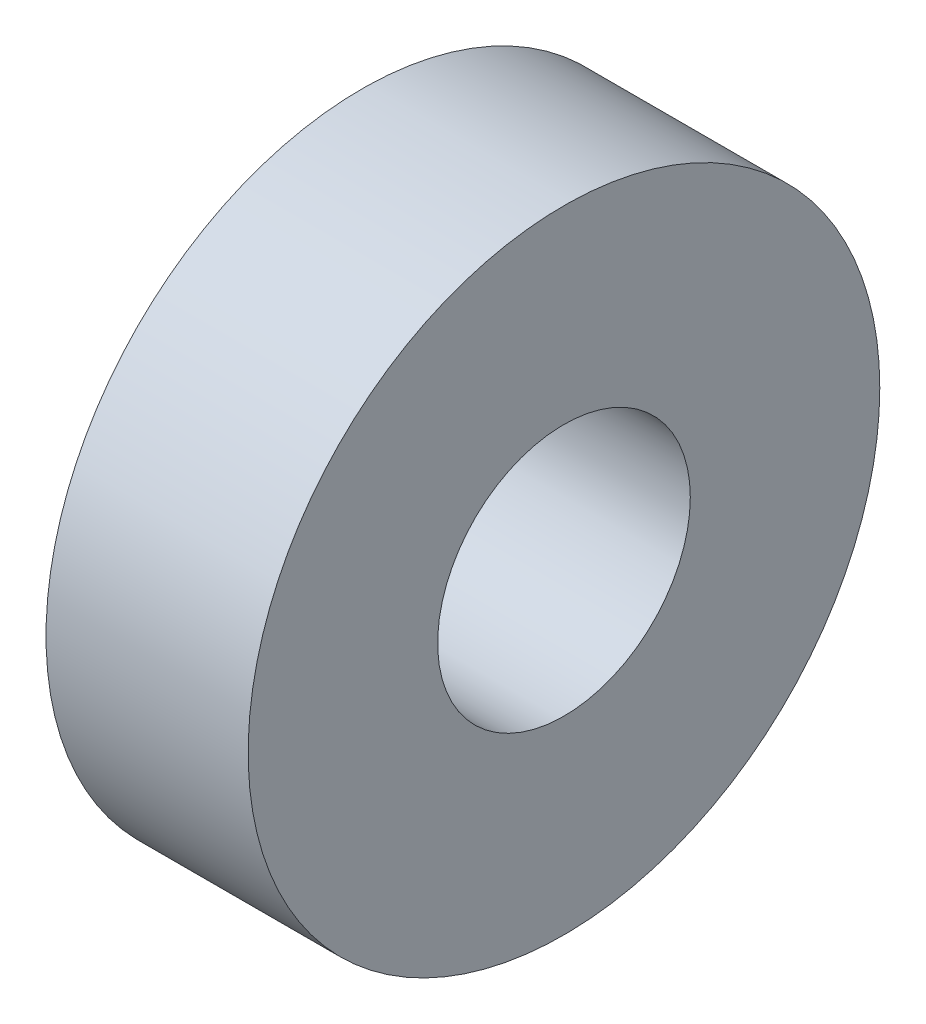
SolidWorks part; units mm, degrees
ref_plane "前视基准面" through (0, 0, 0) normal (0, 0, 1) x (1, 0, 0)
ref_plane "上视基准面" through (0, 0, 0) normal (0, 1, 0) x (1, 0, 0)
ref_plane "右视基准面" through (0, 0, 0) normal (1, 0, 0) x (0, 0, -1)
sketch "草图1" plane through (0, 0, 0) normal (1, 0, 0) x (0, 0, -1)
  circle A0 centre (0, 0) radius 10
  circle A1 centre (0, 0) radius 25
extrude "凸台-拉伸1" add sketch "草图1" along normal blind 16
